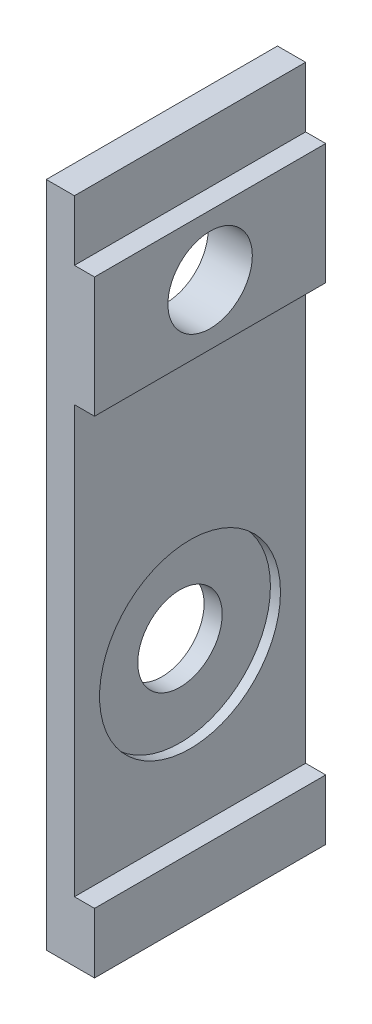
SolidWorks part; units mm, degrees
ref_plane "Alzado" through (0, 0, 0) normal (0, 0, 1) x (1, 0, 0)
ref_plane "Planta" through (0, 0, 0) normal (0, 1, 0) x (1, 0, 0)
ref_plane "Vista lateral" through (0, 0, 0) normal (1, 0, 0) x (0, 0, -1)
sketch "Croquis1" plane through (0, 0, 0) normal (0, 0, 1) x (1, 0, 0)
  line L0 (-89.2534, -13.3365) -> (-89.2534, 19.8635)
  line L1 (-89.2534, 19.8635) -> (-87.8534, 19.8635)
  line L2 (-89.2534, -13.3365) -> (-86.8534, -13.3365)
  line L3 (-86.8534, -13.3365) -> (-86.8534, -10.3365)
  line L4 (-86.8534, -10.3365) -> (-87.8534, -10.3365)
  line L5 (-87.8534, 19.8635) -> (-87.8534, 13.8635) construction
  line L6 (-87.8534, 13.8635) -> (-87.8534, 10.8635) construction
  line L7 (-87.8534, 10.8635) -> (-86.8534, 10.8635)
  line L8 (-86.8534, 10.8635) -> (-86.8534, 16.8635)
  line L9 (-86.8534, 16.8635) -> (-87.8534, 16.8635)
  line L10 (-87.8534, 16.8635) -> (-87.8534, 19.8635)
  line L11 (-87.8534, 10.8635) -> (-87.8534, -10.3365)
  dimension "D1" = 33.2
  dimension "D2" = 1.4
  dimension "D3" = 2.4
  dimension "D4" = 3
  dimension "D5" = 6
extrude "Saliente-Extruir1" add sketch "Croquis1" along normal blind 11.5
sketch "Croquis2" plane through (-86.8534, 0, 0) normal (1, 0, 0) x (0, 0, -1)
  line L0 (-11.5, 10.8635) -> (0, 16.8635) construction
  line L1 (-5.75, -13.3365) -> (-5.75, -2.3365) construction
  line L2 (-11.5, -13.3365) -> (0, -13.3365) construction
  circle A0 centre (-5.75, 13.8635) radius 2.1
  circle A1 centre (-5.75, -2.3365) radius 2.1
  dimension "D1" = 11
  dimension "D2" = 4.2
  dimension "D3" = 4.2
extrude "Cortar-Extruir1" cut sketch "Croquis2" against normal up to vertex
sketch "Croquis3" plane through (-87.8534, 0, 0) normal (1, 0, 0) x (0, 0, -1)
  circle A0 centre (-5.75, -2.3365) radius 4.5
  dimension "D1" = 9
extrude "Cortar-Extruir2" cut sketch "Croquis3" against normal blind 0.5
sketch "Croquis4" plane through (-89.2534, 0, 0) normal (-1, 0, 0) x (0, 0, 1)
  circle A0 centre (5.75, 13.8635) radius 3
  dimension "D1" = 6
extrude "Cortar-Extruir3" cut sketch "Croquis4" against normal blind 0.2
